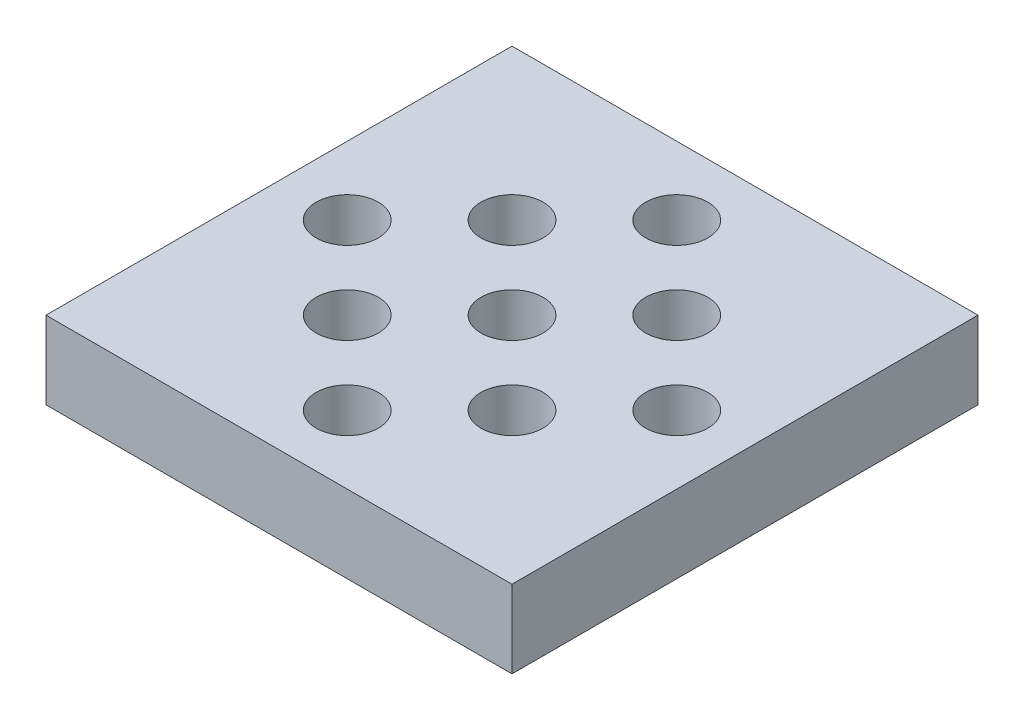
SolidWorks part; units mm, degrees
ref_plane "Front Plane" through (0, 0, 0) normal (0, 0, 1) x (1, 0, 0)
ref_plane "Top Plane" through (0, 0, 0) normal (0, 1, 0) x (1, 0, 0)
ref_plane "Right Plane" through (0, 0, 0) normal (1, 0, 0) x (0, 0, -1)
sketch "Sketch1" plane through (0, 0, 0) normal (0, 1, 0) x (1, 0, 0)
  line L1 (30, -30) -> (-30, -30)
  line L2 (30, -30) -> (30, 30)
  line L3 (30, 30) -> (-30, 30)
  line L4 (-30, -30) -> (-30, 30)
  line L5 (30, -30) -> (-30, 30) construction
  line L6 (30, 30) -> (-30, -30) construction
  point P0 (0, 0)
  dimension "D1" = 60
  dimension "D2" = 60
extrude "Boss-Extrude1" add sketch "Sketch1" along normal blind 10
sketch "Sketch2" plane through (0, 0, 0) normal (0, -1, 0) x (1, 0, 0)
  line L1 (23, 23) -> (-23, 23)
  line L2 (23, 23) -> (23, -23)
  line L3 (23, -23) -> (-23, -23)
  line L4 (-23, 23) -> (-23, -23)
  line L5 (23, 23) -> (-23, -23) construction
  line L6 (23, -23) -> (-23, 23) construction
  circle A2 centre (0, -21.2132) radius 4
  point P0 (0, 0)
  dimension "D3" = 8
  dimension "D4" = 15
  dimension "D5" = 15
  dimension "D1" = 46
  dimension "D2" = 46
extrude "Cut-Extrude1" cut sketch "Sketch2" against normal blind 10 contours L3 A2 | L3 A2
pattern_linear "LPattern1" count 3 spacing 15 along (-0.7071, 0, 0.7071) count 3 spacing 15 along (0.7071, 0, 0.7071) of "Cut-Extrude1"
equation "\"`60\"=139.344"
